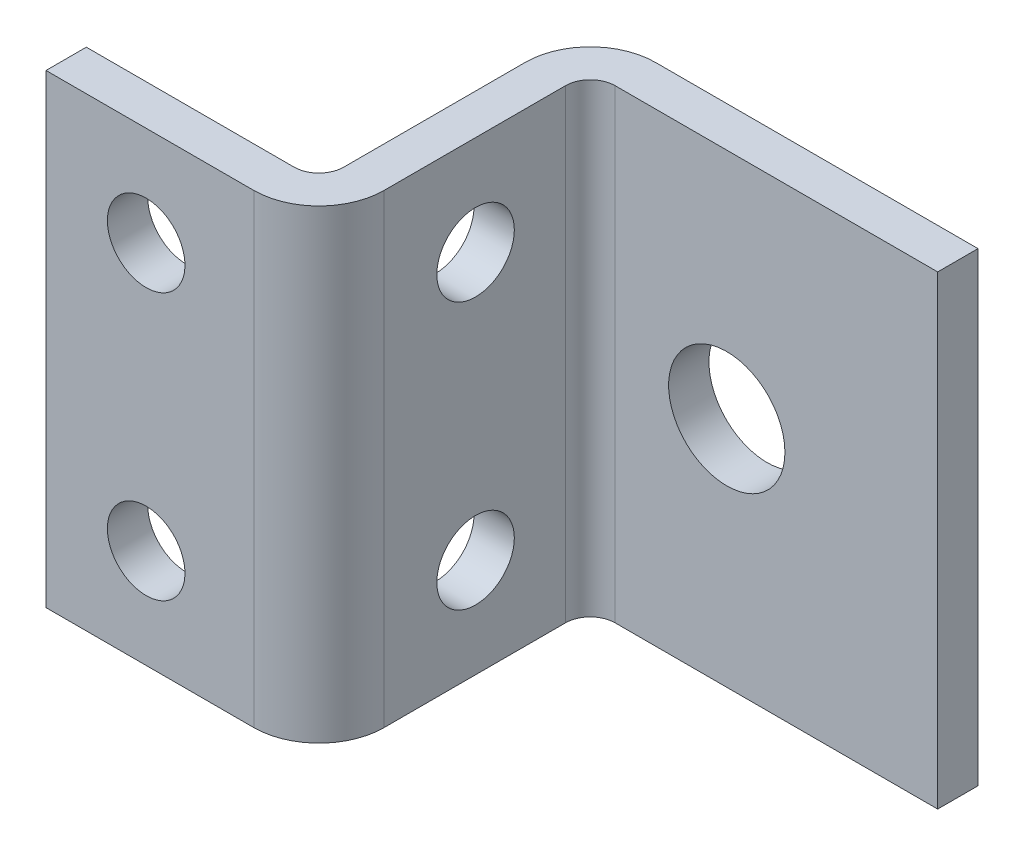
SolidWorks part; units mm, degrees
material "Alloy Steel"
ref_plane "Front" through (0, 0, 0) normal (0, 0, 1) x (1, 0, 0)
ref_plane "Top" through (0, 0, 0) normal (0, 1, 0) x (1, 0, 0)
ref_plane "Right" through (0, 0, 0) normal (1, 0, 0) x (0, 0, -1)
sketch "Sketch1" plane through (0, 0, 0) normal (0, 1, 0) x (1, 0, 0)
  line L0 (0, -22.225) -> (0, 0)
  line L1 (0, 0) -> (31.75, 0)
  line L2 (0, -22.225) -> (-19.05, -22.225)
  dimension "A2" = 31.75
  dimension "A1" = 19.05
  dimension "Offset" = 22.225
extrude "Extrude-Thin1" add sketch "Sketch1" along normal mid plane 38.1 thin
sketch "Sketch4" plane through (-22.225, 0, 25.527) normal (0, 0, -1) x (-1, 0, 0)
  line L0 (-3.175, 19.05) -> (-3.175, -19.05) construction
  line L1 (-11.3792, 10.922) -> (-11.3792, -10.922) construction
  circle A0 centre (-11.3792, 10.922) radius 3.175
  circle A1 centre (-11.3792, -10.922) radius 3.175
  point P8 (-11.3792, 0)
extrude "Extrude3" cut sketch "Sketch4" along normal through all
sketch "Sketch9" plane through (3.302, 0, 0) normal (1, 0, 0) x (0, 0, -1)
  line L0 (-12.7, 10.922) -> (-12.7, -10.922) construction
  line L1 (-22.225, 10.922) -> (-25.527, 10.922) construction
  line L2 (-22.225, -10.922) -> (-25.527, -10.922) construction
  line L3 (0, 19.05) -> (0, -19.05) construction
  circle A0 centre (-12.7, 10.922) radius 3.175
  circle A1 centre (-12.7, -10.922) radius 3.175
  dimension "D1" = 6.35
extrude "Cut-Extrude3" cut sketch "Sketch9" against normal through all
sketch "Sketch8" plane through (0, 0, 3.302) normal (0, 0, 1) x (1, 0, 0)
  line L0 (-55.372, 0) -> (14.478, 0) construction
  line L1 (31.75, 19.05) -> (31.75, -19.05) construction
  circle A0 centre (14.478, 0) radius 4.7625
  circle A1 centre (-55.372, 0) radius 4.7625
  dimension "Hole Size" = 9.525
  dimension "Hole Offset H 2" = 69.85
  dimension "Hole Offset H 1" = 17.272
extrude "Cut-Extrude2" cut sketch "Sketch8" against normal through all
sketch "Sketch10" plane through (0, 0, 0) normal (0, 1, 0) x (1, 0, 0)
  line L4 (3.302, -9.525) -> (0, -9.525) construction
  line L5 (0, -15.875) -> (3.302, -15.875) construction
  line L6 (3.302, -9.525) -> (0, -9.525)
  line L7 (0, -15.875) -> (3.302, -15.875)
  line L8 (-1.016, -12.7) -> (4.318, -12.7)
  line L9 (0, -12.7) -> (3.302, -12.7) construction
  line L10 (0, -20.193) -> (0, -5.334) construction
  point P8 (1.651, -9.525)
  point P9 (1.651, -12.7)
  dimension "D1" = 1.016
equation "\"D1@Sketch9\" = \"Hole Size@Sketch4\""
